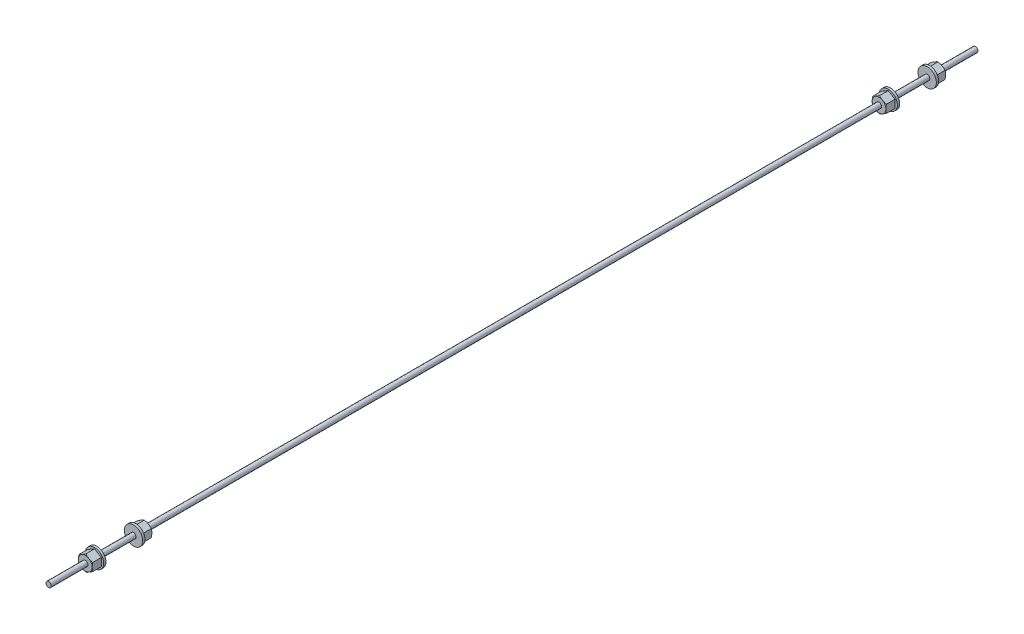
SolidWorks part; units mm, degrees
material "AISI 304"
ref_plane "Front Plane" through (0, 0, 0) normal (0, 0, 1) x (1, 0, 0)
ref_plane "Top Plane" through (0, 0, 0) normal (0, 1, 0) x (1, 0, 0)
ref_plane "Right Plane" through (0, 0, 0) normal (1, 0, 0) x (0, 0, -1)
sketch "Sketch1" plane through (0, 0, 0) normal (0, 0, 1) x (1, 0, 0)
  line L1 (0, 5.4993) -> (-4.7625, 2.7496)
  line L2 (-4.7625, 2.7496) -> (-4.7625, -2.7496)
  line L3 (-4.7625, -2.7496) -> (0, -5.4993)
  line L4 (0, -5.4993) -> (4.7625, -2.7496)
  line L5 (4.7625, -2.7496) -> (4.7625, 2.7496)
  line L6 (4.7625, 2.7496) -> (0, 5.4993)
  circle A0 centre (0, 0) radius 4.7625 construction
  dimension "Hex" = 9.525
extrude "Extrude1" add sketch "Sketch1" against normal blind 7.9375
sketch "Sketch13" plane through (0, 0, -7.9375) normal (0, 0, -1) x (-1, 0, 0)
  circle A0 centre (0, 0) radius 6.35
  dimension "Flange od" = 12.7
extrude "Extrude3" add sketch "Sketch13" against normal blind 1.5875
sketch "Sketch2" plane through (0, 0, 0) normal (0, 0, 1) x (1, 0, 0)
  circle A0 centre (0, 0) radius 4.7625 construction
  circle A1 centre (0, 0) radius 4.7625
extrude "Cut-Extrude1" cut sketch "Sketch2" against normal through all draft 60 flip side to cut
sketch "Sketch4" plane through (0, 0, 0) normal (0, 0, 1) x (1, 0, 0)
  circle A0 centre (0, 0) radius 1.8161
  dimension "Thread Dia" = 3.6322
sketch "Sketch14" plane through (0, 0, -7.9375) normal (0, 0, -1) x (-1, 0, 0)
  circle A0 centre (0, 0) radius 1.8161
  dimension "D1" = 3.6322
extrude "Boss-Extrude1" add sketch "Sketch14" along normal blind 12.7
ref_plane "Plane1" through (0, 0, -20.6375) normal (0, 0, -1) x (-1, 0, 0)
mirror "Mirror1" about plane through (0, 0, -20.6375) normal (0, 0, -1) of "Extrude3", "Cut-Extrude1", "Extrude1", "Boss-Extrude1"
sketch "Sketch15" plane through (0, 0, -41.275) normal (0, 0, -1) x (-1, 0, 0)
  circle A0 centre (0, 0) radius 1.8161
  dimension "D1" = 3.6322
extrude "Boss-Extrude2" add sketch "Sketch15" along normal blind 254
ref_plane "Plane2" through (0, 0, -295.275) normal (0, 0, -1) x (-1, 0, 0)
mirror "Mirror2" about plane through (0, 0, -295.275) normal (0, 0, -1) of "Extrude3", "Cut-Extrude1", "Extrude1", "Boss-Extrude1", "Mirror1", "Boss-Extrude2"
sketch "Sketch16" plane through (0, 0, -590.55) normal (0, 0, -1) x (-1, 0, 0)
  circle A0 centre (0, 0) radius 1.8161
  dimension "D1" = 3.6322
extrude "Boss-Extrude3" add sketch "Sketch16" along normal blind 25.4
extrude "Boss-Extrude4" add sketch "Sketch4" along normal blind 25.4
